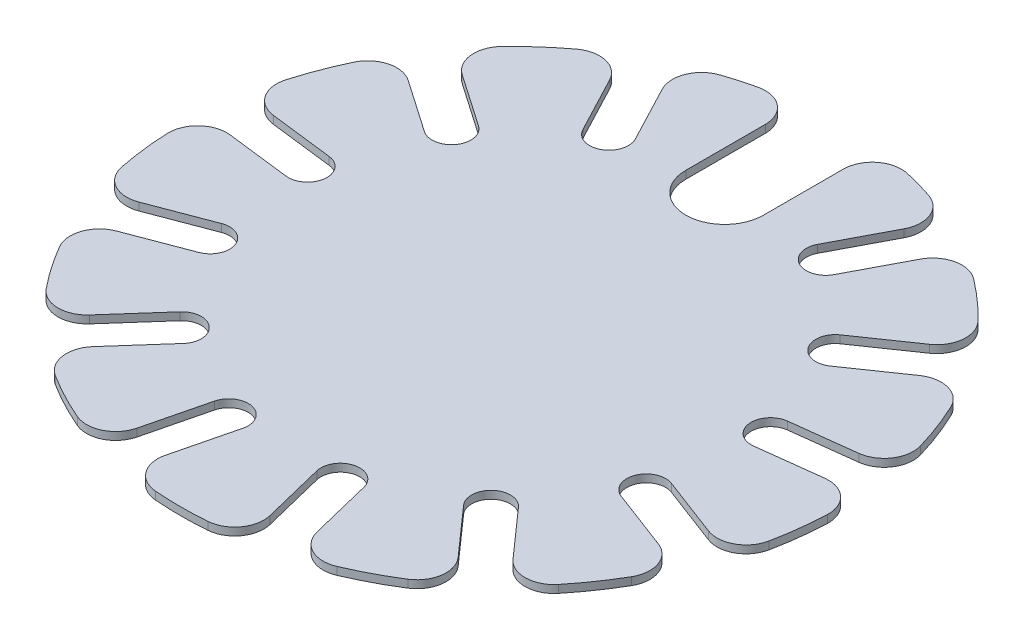
SolidWorks part; units mm, degrees
material "Polybutadiene (PB)"
ref_plane "Front Plane" through (0, 0, 0) normal (0, 0, 1) x (1, 0, 0)
ref_plane "Top Plane" through (0, 0, 0) normal (0, 1, 0) x (1, 0, 0)
ref_plane "Right Plane" through (0, 0, 0) normal (1, 0, 0) x (0, 0, -1)
sketch "Sketch1" plane through (0, 0, 0) normal (0, 1, 0) x (1, 0, 0)
  line L0 (-0.5, 6) -> (-0.5, 8.4853)
  line L1 (0.5, 6) -> (0.5, 8.4853)
  line L2 (2.3456, 5.5451) -> (3.5006, 7.7457)
  line L3 (3.2311, 5.0804) -> (4.386, 7.281)
  line L4 (4.6539, 3.8199) -> (6.6992, 5.2317)
  line L5 (5.2219, 2.9969) -> (7.2673, 4.4087)
  line L6 (5.896, 1.2196) -> (8.3631, 1.5191)
  line L7 (6.0165, 0.2269) -> (8.4837, 0.5264)
  line L8 (5.7874, -1.6601) -> (8.1112, -2.5414)
  line L9 (5.4328, -2.5951) -> (7.7566, -3.4764)
  line L10 (4.353, -4.1595) -> (6.001, -6.0198)
  line L11 (3.6045, -4.8226) -> (5.2525, -6.6829)
  line L12 (1.9214, -5.706) -> (2.5161, -8.1191)
  line L13 (0.9504, -5.9453) -> (1.5452, -8.3584)
  line L14 (-0.9504, -5.9453) -> (-1.5452, -8.3584)
  line L15 (-1.9214, -5.706) -> (-2.5161, -8.1191)
  line L16 (-3.6045, -4.8226) -> (-5.2525, -6.6829)
  line L17 (-4.353, -4.1595) -> (-6.001, -6.0198)
  line L18 (-5.4328, -2.5951) -> (-7.7566, -3.4764)
  line L19 (-5.7874, -1.6601) -> (-8.1112, -2.5414)
  line L20 (-6.0165, 0.2269) -> (-8.4837, 0.5264)
  line L21 (-5.896, 1.2196) -> (-8.3631, 1.5191)
  line L22 (-5.2219, 2.9969) -> (-7.2673, 4.4087)
  line L23 (-4.6539, 3.8199) -> (-6.6992, 5.2317)
  line L24 (-3.2311, 5.0804) -> (-4.386, 7.281)
  line L25 (-2.3456, 5.5451) -> (-3.5006, 7.7457)
  arc A0 (-0.5, 8.4853) -> (-3.5006, 7.7457) centre (0, 0) ccw
  circle A1 centre (0, 0) radius 6 construction
  arc A2 (-0.5, 6) -> (0.5, 6) centre (0, 6) ccw
  arc A3 (2.3456, 5.5451) -> (3.2311, 5.0804) centre (2.7883, 5.3127) ccw
  arc A4 (4.6539, 3.8199) -> (5.2219, 2.9969) centre (4.9379, 3.4084) ccw
  arc A5 (5.896, 1.2196) -> (6.0165, 0.2269) centre (5.9563, 0.7232) ccw
  arc A6 (5.7874, -1.6601) -> (5.4328, -2.5951) centre (5.6101, -2.1276) ccw
  arc A7 (4.353, -4.1595) -> (3.6045, -4.8226) centre (3.9787, -4.4911) ccw
  arc A8 (1.9214, -5.706) -> (0.9504, -5.9453) centre (1.4359, -5.8257) ccw
  arc A9 (-0.9504, -5.9453) -> (-1.9214, -5.706) centre (-1.4359, -5.8257) ccw
  arc A10 (-3.6045, -4.8226) -> (-4.353, -4.1595) centre (-3.9787, -4.4911) ccw
  arc A11 (-5.4328, -2.5951) -> (-5.7874, -1.6601) centre (-5.6101, -2.1276) ccw
  arc A12 (-6.0165, 0.2269) -> (-5.896, 1.2196) centre (-5.9563, 0.7232) ccw
  arc A13 (-5.2219, 2.9969) -> (-4.6539, 3.8199) centre (-4.9379, 3.4084) ccw
  arc A14 (-3.2311, 5.0804) -> (-2.3456, 5.5451) centre (-2.7883, 5.3127) ccw
  arc A15 (-4.386, 7.281) -> (-6.6992, 5.2317) centre (0, 0) ccw
  arc A16 (-7.2673, 4.4087) -> (-8.3631, 1.5191) centre (0, 0) ccw
  arc A17 (-8.4837, 0.5264) -> (-8.1112, -2.5414) centre (0, 0) ccw
  arc A18 (-7.7566, -3.4764) -> (-6.001, -6.0198) centre (0, 0) ccw
  arc A19 (-5.2525, -6.6829) -> (-2.5161, -8.1191) centre (0, 0) ccw
  arc A20 (-1.5452, -8.3584) -> (1.5452, -8.3584) centre (0, 0) ccw
  arc A21 (2.5161, -8.1191) -> (5.2525, -6.6829) centre (0, 0) ccw
  arc A22 (6.001, -6.0198) -> (7.7566, -3.4764) centre (0, 0) ccw
  arc A23 (8.1112, -2.5414) -> (8.4837, 0.5264) centre (0, 0) ccw
  arc A24 (8.3631, 1.5191) -> (7.2673, 4.4087) centre (0, 0) ccw
  arc A25 (3.5006, 7.7457) -> (0.5, 8.4853) centre (0, 0) ccw
  arc A26 (6.6992, 5.2317) -> (4.386, 7.281) centre (0, 0) ccw
  point P70 (0, 0)
  dimension "D1" = 17
  dimension "D2" = 12
  dimension "D3" = 1
  dimension "D4" = 13
extrude "Boss-Extrude1" add sketch "Sketch1" along normal mid plane 0.2
sketch "Sketch2" plane through (0, 0, 0) normal (0, 1, 0) x (1, 0, 0)
  line L10 (-0.5, 6) -> (-0.5, 8.4853) construction
  line L11 (0.5, 8.4853) -> (0.5, 6) construction
  line L12 (-0.5, 6) -> (-0.5, 8.4853) construction
  line L13 (0.5, 8.4853) -> (0.5, 6) construction
  line L14 (-1, 5.5) -> (-1, 8.4853)
  line L15 (1, 8.4853) -> (1, 5.5)
  line L16 (-1, 6) -> (-1, 8.4853) construction
  line L18 (-1, 5.5) -> (1, 5.5) construction
  line L19 (1, 8.4853) -> (-1, 8.4853)
  arc A3 (-0.5, 6) -> (0.5, 6) centre (0, 6) ccw construction
  arc A4 (-0.5, 6) -> (0.5, 6) centre (0, 6) ccw construction
  arc A5 (-1, 5.5) -> (1, 5.5) centre (0, 5.5) ccw
  dimension "D1" = 0.5
extrude "Cut-Extrude1" cut sketch "Sketch2" against normal through all both and the other way through all
fillet "Fillet1" radius 0.75 26 edges at (4.386, 0, -7.281) (6.6992, 0, -5.2317) (7.2673, 0, -4.4087) (8.3631, 0, -1.5191) (8.4837, 0, -0.5264) (8.1112, 0, 2.5414) (7.7566, 0, 3.4764) (6.001, 0, 6.0198) (5.2525, 0, 6.6829) (2.5161, 0, 8.1191) (1.5452, 0, 8.3584) (-1.5452, 0, 8.3584) (-2.5161, 0, 8.1191) (-5.2525, 0, 6.6829) (-6.001, 0, 6.0198) (-7.7566, 0, 3.4764) (-8.1112, 0, 2.5414) (-8.4837, 0, -0.5264) (-8.3631, 0, -1.5191) (-7.2673, 0, -4.4087) (-6.6992, 0, -5.2317) (-4.386, 0, -7.281) (-3.5006, 0, -7.7457) (3.5006, 0, -7.7457) (1, 0, -8.441) (-1, 0, -8.441)
